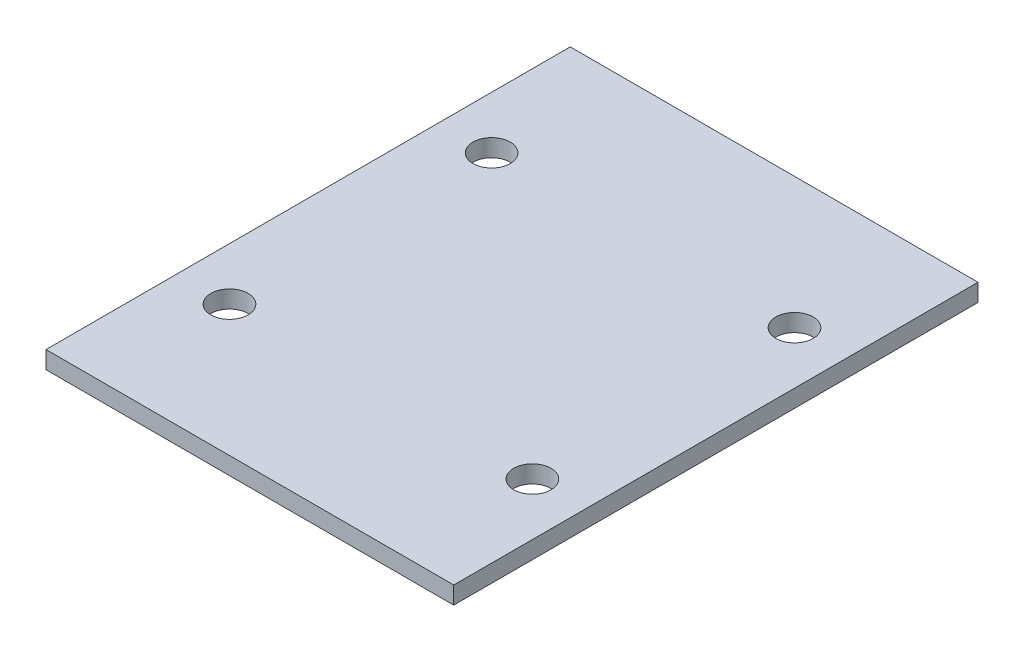
SolidWorks part; units mm, degrees
ref_plane "Alzado" through (0, 0, 0) normal (0, 0, 1) x (1, 0, 0)
ref_plane "Planta" through (0, 0, 0) normal (0, 1, 0) x (1, 0, 0)
ref_plane "Vista lateral" through (0, 0, 0) normal (1, 0, 0) x (0, 0, -1)
sketch "Croquis1" plane through (0, 0, 0) normal (0, 1, 0) x (1, 0, 0)
  line L1 (-35, -45) -> (35, -45)
  line L2 (-35, -45) -> (-35, 45)
  line L3 (-35, 45) -> (35, 45)
  line L4 (35, -45) -> (35, 45)
  line L5 (-35, -45) -> (35, 45) construction
  line L6 (-35, 45) -> (35, -45) construction
  point P0 (0, 0)
  dimension "D1" = 70
  dimension "D2" = 90
extrude "Saliente-Extruir1" add sketch "Croquis1" along normal blind 3
hole_wizard "Taladro de margen para M61" positions "Croquis2" profile "Croquis4" hole size "M6" standard "ISO" end condition through all
sketch "Croquis2" plane through (0, 3, 0) normal (0, 1, 0) x (1, 0, 0)
  line L0 (-1000, 0) -> (49000, 0) construction
  line L1 (0, -1000) -> (0, 49000) construction
  point P0 (-26, 22.5)
  point P11 (26, 22.5)
  point P12 (26, -22.5)
  point P13 (-26, -22.5)
  dimension "D1" = 52
  dimension "D2" = 45
sketch "Croquis4" plane through (-26, 3, -22.5) normal (1, 0, 0) x (0, 0, 1)
  line L0 (0, 0) -> (0, 3)
  line L1 (0, 3) -> (3.2, 3)
  line L2 (3.2, 3) -> (3.2, 0)
  line L5 (3.2, 0) -> (0, 0)
  line L11 (0, -6.35) -> (0, 107.95) construction
  dimension "Diámetro de taladro hasta el siguiente" = 6.4
  dimension "Profundidad de taladro hasta el siguiente" = 3
